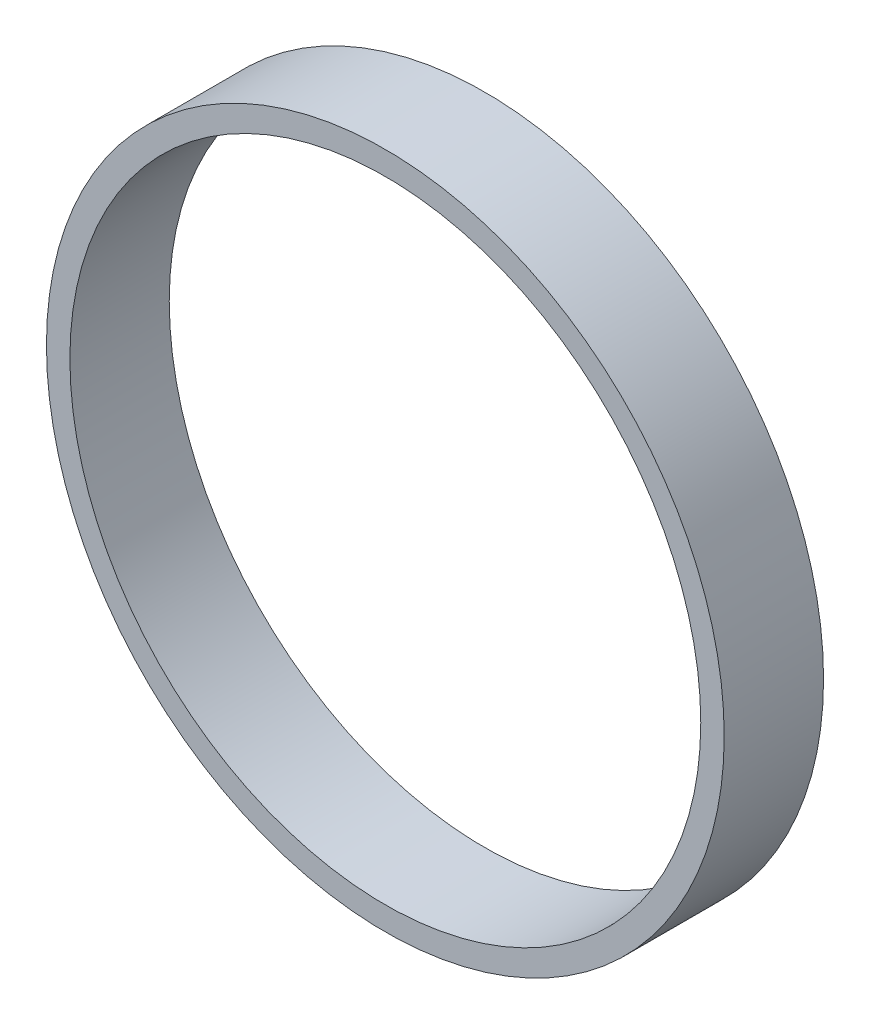
SolidWorks part; units mm, degrees
ref_plane "Front Plane" through (0, 0, 0) normal (0, 0, 1) x (1, 0, 0)
ref_plane "Top Plane" through (0, 0, 0) normal (0, 1, 0) x (1, 0, 0)
ref_plane "Right Plane" through (0, 0, 0) normal (1, 0, 0) x (0, 0, -1)
sketch "Sketch1" plane through (0, 0, 0) normal (0, 0, 1) x (1, 0, 0)
  circle A0 centre (0, 0) radius 31.75
  circle A1 centre (0, 0) radius 34.11
  dimension "D1" = 63.5
  dimension "D2" = 68.22
extrude "Boss-Extrude1" add sketch "Sketch1" along normal blind 10
